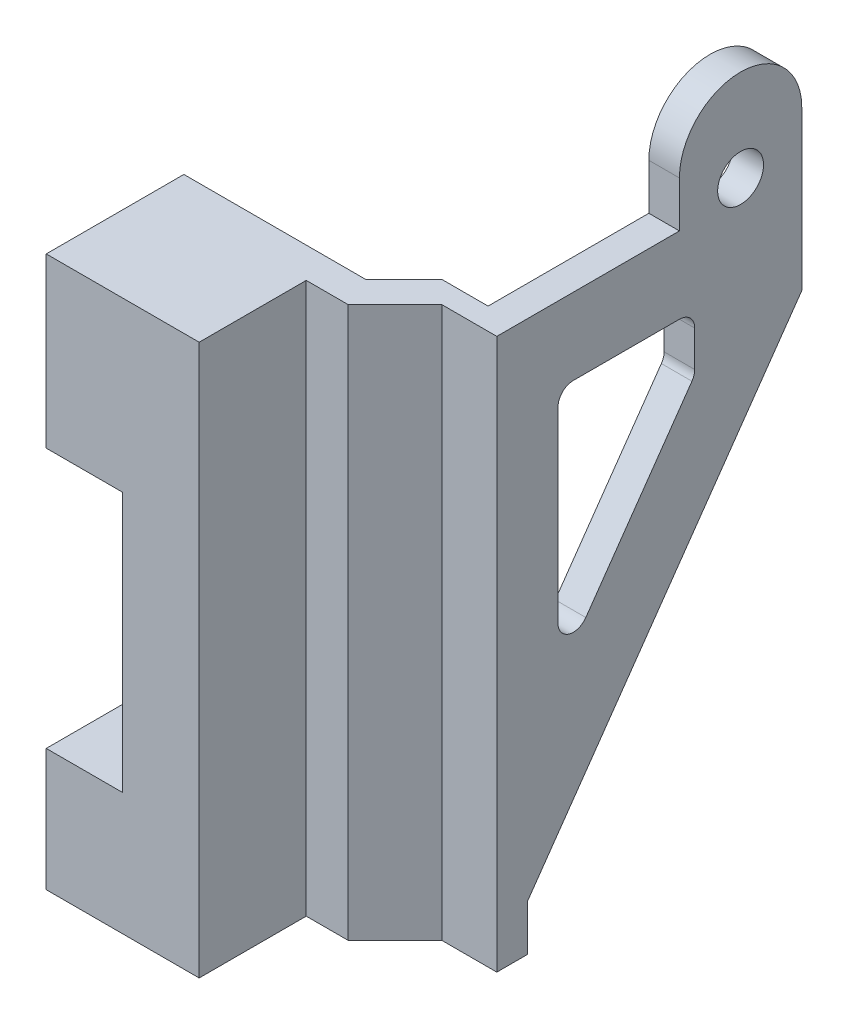
SolidWorks part; units mm, degrees
ref_plane "Front Plane" through (0, 0, 0) normal (0, 0, 1) x (1, 0, 0)
ref_plane "Top Plane" through (0, 0, 0) normal (0, 1, 0) x (1, 0, 0)
ref_plane "Right Plane" through (0, 0, 0) normal (1, 0, 0) x (0, 0, -1)
sketch "Sketch1" plane through (0, 0, 0) normal (0, 1, 0) x (1, 0, 0)
  line L0 (0, 0) -> (11.9097, 0)
  line L1 (11.9097, 0) -> (14.3993, 2.4897)
  line L2 (14.3993, 2.4897) -> (17.3993, 2.4897)
  line L3 (17.3993, 2.4897) -> (17.3993, 21)
  line L4 (0, 0) -> (0, -9)
  line L5 (0, -9) -> (10, -9)
  line L6 (10, -9) -> (10, -2)
  line L7 (10, -2) -> (12.7381, -2)
  line L8 (12.7381, -2) -> (15.7993, 1.0612)
  line L9 (15.7993, 1.0612) -> (19.3993, 1.0612)
  line L10 (19.3993, 1.0612) -> (19.3993, 21)
  line L11 (19.3993, 21) -> (17.3993, 21)
  dimension "D1" = 10
  dimension "D2" = 2.7381
  dimension "D3" = 4.3292
  dimension "D4" = 3
  dimension "D5" = 3.6
  dimension "D6" = 2
  dimension "D7" = 2
  dimension "D8" = 2
  dimension "D9" = 9
  dimension "D10" = 30
  dimension "D11" = 135
extrude "Boss-Extrude1" add sketch "Sketch1" along normal blind 36
sketch "Sketch2" plane through (19.3993, 0, 0) normal (1, 0, 0) x (0, 0, -1)
  line L0 (3.0612, 0) -> (3.0612, 3)
  line L1 (1.0612, 0) -> (21, 0) construction
  line L2 (3.0612, 3) -> (21, 28.6192)
  line L3 (21, 36) -> (21, 0) construction
  line L4 (1.0612, 36) -> (1.0612, 0) construction
  line L5 (3.0612, 0) -> (21, 0)
  line L6 (21, 28.6192) -> (21, 0)
  dimension "D1" = 2
  dimension "D2" = 3
  dimension "D3" = 145
extrude "Cut-Extrude1" cut sketch "Sketch2" against normal up to next
sketch "Sketch3" plane through (19.3993, 0, 0) normal (1, 0, 0) x (0, 0, -1)
  line L0 (5.0612, 17.7451) -> (5.0612, 30)
  line L1 (6.0612, 31) -> (13, 31)
  line L2 (14, 30) -> (14, 27.6547)
  line L3 (13.8192, 27.0811) -> (6.8804, 17.1715)
  line L4 (21, 28.6192) -> (3.0612, 3) construction
  line L5 (21, 36) -> (21, 28.6192) construction
  line L7 (1.0612, 36) -> (21, 36) construction
  line L8 (1.0612, 36) -> (1.0612, 0) construction
  arc A0 (5.0612, 17.7451) -> (6.8804, 17.1715) centre (6.0612, 17.7451) ccw
  arc A1 (5.0612, 30) -> (6.0612, 31) centre (6.0612, 30) cw
  arc A2 (14, 27.6547) -> (13.8192, 27.0811) centre (13, 27.6547) cw
  arc A3 (13, 31) -> (14, 30) centre (13, 30) cw
  dimension "D5" = 1
  dimension "D1" = 5
  dimension "D2" = 5
  dimension "D3" = 4
  dimension "D4" = 7
extrude "Cut-Extrude2" cut sketch "Sketch3" against normal up to next
sketch "Sketch4" plane through (19.3993, 0, 0) normal (1, 0, 0) x (0, 0, -1)
  line L0 (21, 36) -> (21, 39)
  line L1 (13, 36) -> (13, 39)
  line L6 (1.0612, 0) -> (3.0612, 0)
  line L7 (3.0612, 0) -> (3.0612, 3)
  line L8 (3.0612, 3) -> (21, 28.6192)
  line L9 (21, 28.6192) -> (21, 36)
  line L10 (21, 36) -> (1.0612, 36)
  line L11 (1.0612, 36) -> (1.0612, 0)
  line L16 (21, 36) -> (13, 36)
  arc A0 (21, 39) -> (13, 39) centre (17, 39) ccw
  dimension "D3" = 4
  dimension "D2" = 3
  dimension "D1" = 0
extrude "Boss-Extrude2" add sketch "Sketch4" against normal blind 2
sketch "Sketch5" plane through (19.3993, 0, 0) normal (1, 0, 0) x (0, 0, -1)
  line L2 (13, 39) -> (13, 36) construction
  circle A1 centre (17, 37) radius 1.5
  dimension "D1" = 3
  dimension "D2" = 1
  dimension "D3" = 4
extrude "Cut-Extrude3" cut sketch "Sketch5" against normal up to next
sketch "Sketch6" plane through (0, 0, 0) normal (0, 0, -1) x (-1, 0, 0)
  line L0 (0, 8) -> (-5, 8)
  line L1 (-5, 8) -> (-5, 25)
  line L2 (-5, 25) -> (0, 25)
  line L3 (-11.9097, 36) -> (0, 36) construction
  line L4 (-11.9097, 0) -> (0, 0)
  line L5 (0, 0) -> (0, 36)
  line L6 (0, 36) -> (-11.9097, 36)
  line L7 (-11.9097, 36) -> (-11.9097, 0)
  line L9 (0, 8) -> (0, 25)
  dimension "D2" = 17
  dimension "D3" = 5
  dimension "D4" = 11
  dimension "D1" = 0
extrude "Cut-Extrude4" cut sketch "Sketch6" against normal up to next
